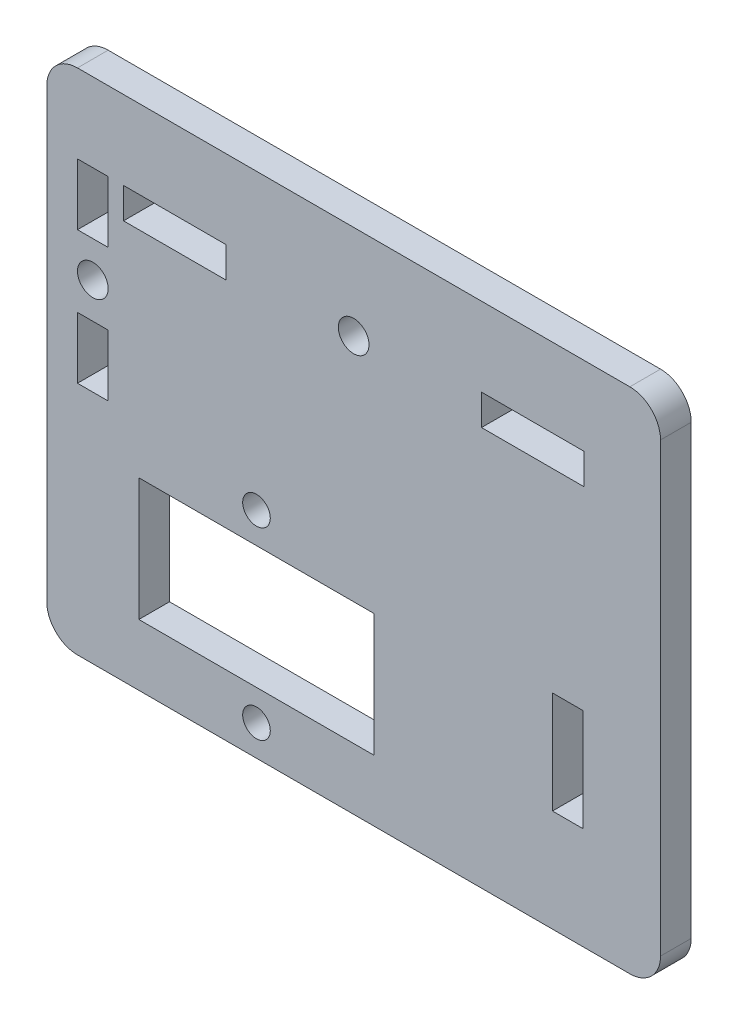
SolidWorks part; units mm, degrees
ref_plane "Front Plane" through (0, 0, 0) normal (0, 0, 1) x (1, 0, 0)
ref_plane "Top Plane" through (0, 0, 0) normal (0, 1, 0) x (1, 0, 0)
ref_plane "Right Plane" through (0, 0, 0) normal (1, 0, 0) x (0, 0, -1)
sketch "Model" plane through (0, 0, 0) normal (0, 0, 1) x (1, 0, 0)
  line L0 (77.3504, 38.9328) -> (77.3504, 61.8479)
  line L1 (77.3503, 18.1479) -> (77.3504, 38.9328)
  line L2 (74.3503, 15.1479) -> (32.8506, 15.1481)
  line L3 (17.3505, 61.8485) -> (17.3503, 19.0355)
  line L4 (23.3505, 44.1482) -> (23.3504, 38.1482)
  line L5 (20.3505, 44.1482) -> (23.3505, 44.1482)
  line L6 (20.3504, 38.1482) -> (20.3505, 44.1482)
  line L7 (23.3504, 38.1482) -> (20.3504, 38.1482)
  line L8 (23.3505, 57.1482) -> (23.3505, 51.1482)
  line L9 (20.3505, 57.1482) -> (23.3505, 57.1482)
  line L10 (20.3505, 51.1482) -> (20.3505, 57.1482)
  line L11 (23.3505, 51.1482) -> (20.3505, 51.1482)
  line L12 (49.3503, 21.148) -> (49.3504, 33.148)
  line L13 (26.3503, 21.1482) -> (49.3503, 21.148)
  line L14 (26.3504, 33.1482) -> (26.3503, 21.1482)
  line L15 (49.3504, 33.148) -> (26.3504, 33.1482)
  line L16 (34.8505, 54.1481) -> (34.8505, 57.1481)
  line L17 (24.8505, 54.1482) -> (34.8505, 54.1481)
  line L18 (24.8505, 57.1482) -> (24.8505, 54.1482)
  line L19 (34.8505, 57.1481) -> (24.8505, 57.1482)
  line L20 (69.8505, 54.1479) -> (69.8505, 57.1479)
  line L21 (59.8505, 54.1479) -> (69.8505, 54.1479)
  line L22 (59.8505, 57.148) -> (59.8505, 54.1479)
  line L23 (69.8505, 57.1479) -> (59.8505, 57.148)
  line L25 (69.7853, 25.1479) -> (66.7853, 25.1479)
  line L26 (69.7853, 25.1479) -> (69.7853, 35.1479)
  line L27 (69.7853, 35.1479) -> (66.7853, 35.1479)
  line L28 (66.7853, 25.1479) -> (66.7853, 35.1479)
  line L32 (17.3505, 61.8485) -> (17.3505, 58.8511)
  line L33 (73.8505, 64.8479) -> (20.3505, 64.8482)
  line L34 (17.3503, 19.0355) -> (17.3503, 18.1482)
  line L35 (73.8505, 64.8479) -> (74.3505, 64.8479)
  line L36 (20.3503, 15.1482) -> (32.8506, 15.1481)
  circle A1 centre (47.3505, 55.648) radius 1.5
  circle A2 centre (37.8503, 18.1481) radius 1.35
  circle A3 centre (37.8504, 36.1481) radius 1.35
  circle A4 centre (21.8505, 47.6482) radius 1.5
  arc A5 (20.3505, 64.8482) -> (17.3505, 61.8485) centre (20.3503, 61.8485) ccw
  arc A6 (17.3503, 18.1482) -> (20.3503, 15.1482) centre (20.3499, 18.1477) ccw
  arc A7 (77.3504, 61.8479) -> (74.3505, 64.8479) centre (74.3505, 61.8479) ccw
  arc A8 (74.3503, 15.1479) -> (77.3503, 18.1479) centre (74.3504, 18.1478) ccw
  dimension "D1" = 3
  dimension "D2" = 10
  dimension "D3" = 7.7
  dimension "D4" = 3
  dimension "D5" = 10
  dimension "D6" = 19
extrude "Boss-Extrude1" add sketch "Model" along normal blind 3
